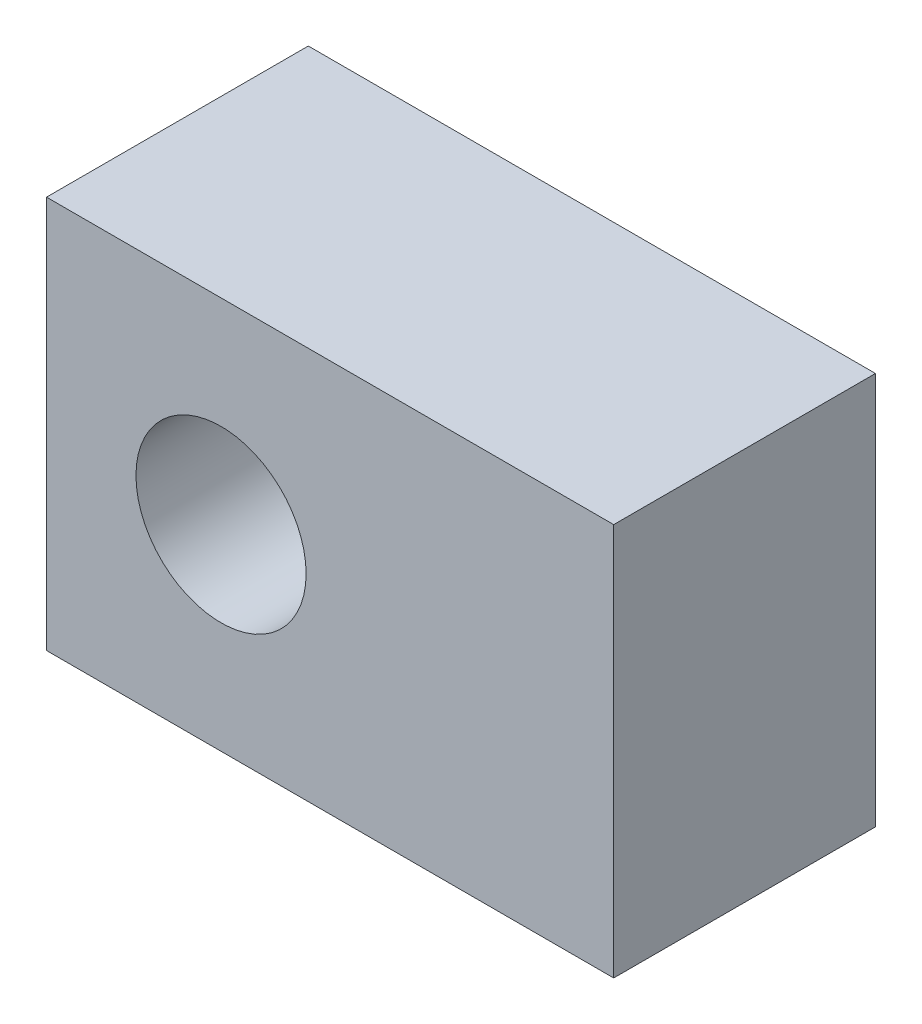
SolidWorks part; units mm, degrees
ref_plane "Front Plane" through (0, 0, 0) normal (0, 0, 1) x (1, 0, 0)
ref_plane "Top Plane" through (0, 0, 0) normal (0, 1, 0) x (1, 0, 0)
ref_plane "Right Plane" through (0, 0, 0) normal (1, 0, 0) x (0, 0, -1)
sketch "Sketch1" plane through (0, 0, 0) normal (0, 0, 1) x (1, 0, 0)
  line L1 (-14.8456, 8.8233) -> (-1.8456, 8.8233)
  line L2 (-14.8456, 8.8233) -> (-14.8456, -0.1767)
  line L3 (-14.8456, -0.1767) -> (-1.8456, -0.1767)
  line L4 (-1.8456, 8.8233) -> (-1.8456, -0.1767)
  dimension "D1" = 13
  dimension "D2" = 9
extrude "Extrude1" add sketch "Sketch1" along normal blind 6
sketch "Sketch2" plane through (0, 0, 6) normal (0, 0, 1) x (1, 0, 0)
  line L0 (-14.8456, 8.8233) -> (-14.8456, -0.1767) construction
  circle A0 centre (-10.8456, 4.3233) radius 1.95
  point P4 (-14.8456, 4.3233)
  point P5 (-14.8456, 4.3233)
  dimension "D1" = 3.9
  dimension "D2" = 4
extrude "Extrude2" cut sketch "Sketch2" against normal blind 16
